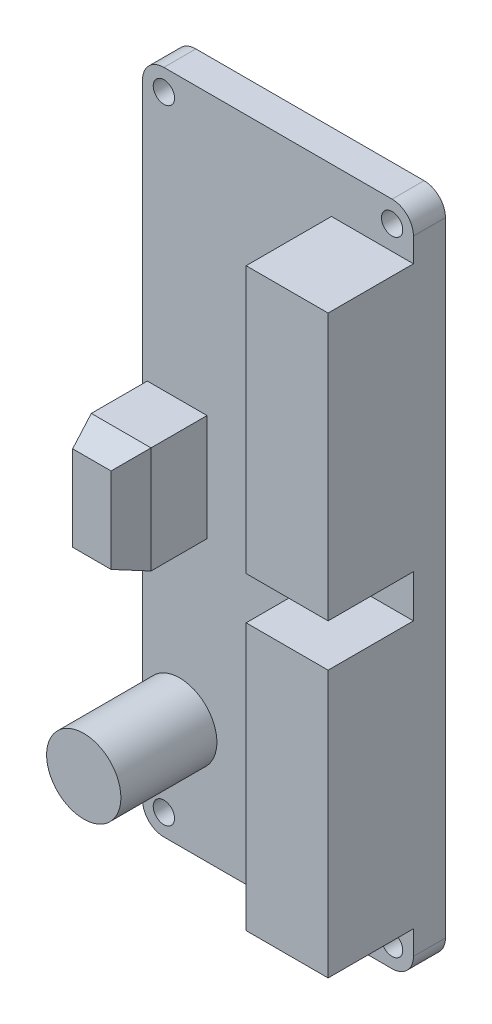
SolidWorks part; units mm, degrees
ref_plane "Ön Düzlem" through (0, 0, 0) normal (0, 0, 1) x (1, 0, 0)
ref_plane "Üst Düzlem" through (0, 0, 0) normal (0, 1, 0) x (1, 0, 0)
ref_plane "Sağ Düzlem" through (0, 0, 0) normal (1, 0, 0) x (0, 0, -1)
sketch "Sketch1" plane through (0, 0, 0) normal (0, 0, 1) x (1, 0, 0)
  line L1 (-10.7, 31.25) -> (10.7, 31.25)
  line L2 (-12.7, 29.25) -> (-12.7, -29.25)
  line L3 (-10.7, -31.25) -> (10.7, -31.25)
  line L4 (12.7, 29.25) -> (12.7, -29.25)
  line L5 (-12.7, 31.25) -> (12.7, -31.25) construction
  line L6 (-12.7, -31.25) -> (12.7, 31.25) construction
  arc A0 (-10.7, -31.25) -> (-12.7, -29.25) centre (-10.7, -29.25) cw
  arc A1 (12.7, -29.25) -> (10.7, -31.25) centre (10.7, -29.25) cw
  arc A2 (12.7, 29.25) -> (10.7, 31.25) centre (10.7, 29.25) ccw
  arc A3 (-10.7, 31.25) -> (-12.7, 29.25) centre (-10.7, 29.25) ccw
  point P0 (0, 0)
  dimension "D3" = 2
  dimension "D4" = 2
  dimension "D1" = 62.5
  dimension "D2" = 25.4
extrude "Boss-Extrude2" add sketch "Sketch1" along normal blind 3
sketch "Sketch2" plane through (0, 0, 3) normal (0, 0, 1) x (1, 0, 0)
  line L0 (0, 0) -> (0, 18.1612) construction
  line L1 (0, 0) -> (18.1259, 0) construction
  circle A0 centre (-10.7, 29.25) radius 1
  circle A1 centre (10.7, 29.25) radius 1
  circle A2 centre (10.7, -29.25) radius 1
  circle A3 centre (-10.7, -29.25) radius 1
  dimension "D1" = 2
extrude "Cut-Extrude1" cut sketch "Sketch2" against normal up to next
sketch "Sketch3" plane through (0, 0, 3) normal (0, 0, 1) x (1, 0, 0)
  line L0 (-12.7, 29.25) -> (-12.7, -29.25) construction
  line L5 (0, 0) -> (-18.6573, 0) construction
  line L7 (-12.2546, -5) -> (-6.6536, -5)
  line L8 (-12.2546, -5) -> (-12.2546, 5)
  line L9 (-12.2546, 5) -> (-6.6536, 5)
  line L10 (-6.6536, -5) -> (-6.6536, 5)
  point P0 (-12.7, 0)
  dimension "D1" = 5
  dimension "D2" = 5
extrude "Boss-Extrude3" add sketch "Sketch3" along normal blind 8
chamfer "Chamfer1" distance 1 angle 70 1 edges at (-9.4541, -5, 11)
chamfer "Chamfer2" distance 1 angle 70 1 edges at (-9.4541, 5, 11)
chamfer "Chamfer3" distance 1 angle 70 1 edges at (-12.2546, 0, 11)
chamfer "Chamfer4" distance 1 angle 70 1 edges at (-6.6536, 0, 11)
sketch "Sketch4" plane through (0, 0, 3) normal (0, 0, 1) x (1, 0, 0)
  line L0 (0, 0) -> (21.6259, 0) construction
  line L1 (12.7, -2) -> (12.7, -27)
  line L2 (12.7, -29.25) -> (12.7, 29.25) construction
  line L3 (12.7, -27) -> (5.0119, -27)
  line L4 (5.0119, -27) -> (5.0119, -2)
  line L5 (5.0119, -2) -> (12.7, -2)
  line L6 (5.0119, 2) -> (12.7, 2)
  line L7 (5.0119, 27) -> (5.0119, 2)
  line L8 (12.7, 27) -> (5.0119, 27)
  line L9 (12.7, 2) -> (12.7, 27)
  dimension "D1" = 2
  dimension "D2" = 25
  dimension "D3" = 7.6881
extrude "Boss-Extrude4" add sketch "Sketch4" along normal blind 8
sketch "Sketch5" plane through (0, 0, 3) normal (0, 0, 1) x (1, 0, 0)
  circle A0 centre (-9.2159, -21.0737) radius 3.4841
extrude "Boss-Extrude5" add sketch "Sketch5" along normal blind 9
